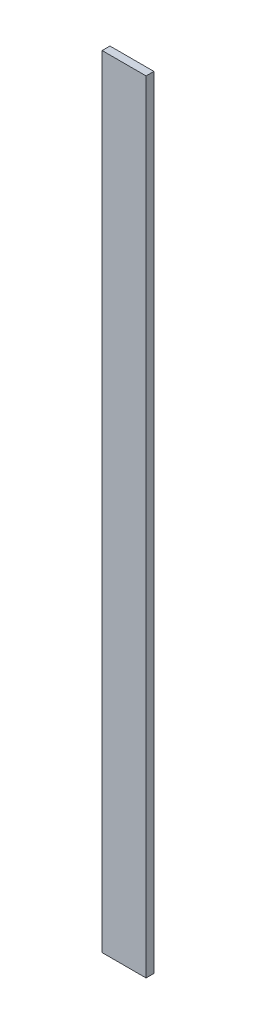
SolidWorks part; units mm, degrees
ref_plane "Front Plane" through (0, 0, 0) normal (0, 0, 1) x (1, 0, 0)
ref_plane "Top Plane" through (0, 0, 0) normal (0, 1, 0) x (1, 0, 0)
ref_plane "Right Plane" through (0, 0, 0) normal (1, 0, 0) x (0, 0, -1)
sketch "Sketch2" plane through (0, 0, 0) normal (0, 0, 1) x (1, 0, 0)
  line L0 (0, 88.2227) -> (0, -88.2227) construction
  line L1 (-7.1438, 168.8279) -> (7.1437, 168.8279)
  line L2 (-7.1438, 168.8279) -> (-7.1437, -85.1721)
  line L3 (-7.1437, -85.1721) -> (7.1437, -85.1721)
  line L4 (7.1437, 168.8279) -> (7.1437, -85.1721)
  dimension "D1" = 14.2875
  dimension "D2" = 254
extrude "Boss-Extrude1" add sketch "Sketch2" along normal blind 2.54
